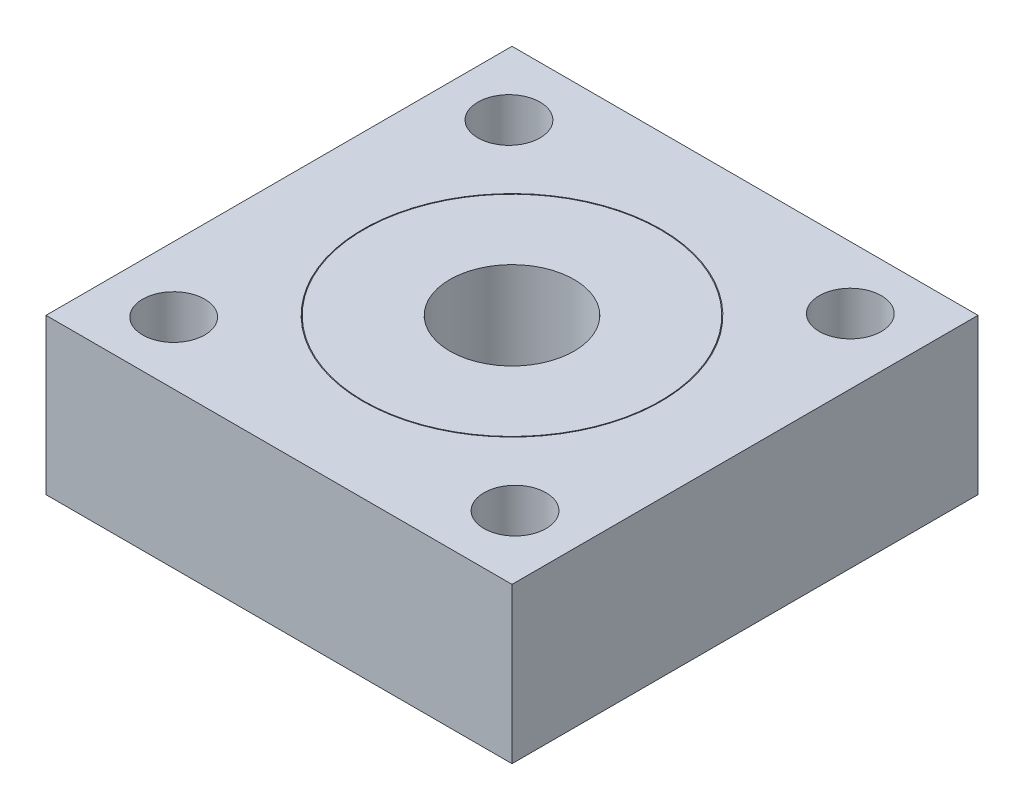
SolidWorks part; units mm, degrees
ref_plane "Front Plane" through (0, 0, 0) normal (0, 0, 1) x (1, 0, 0)
ref_plane "Top Plane" through (0, 0, 0) normal (0, 1, 0) x (1, 0, 0)
ref_plane "Right Plane" through (0, 0, 0) normal (1, 0, 0) x (0, 0, -1)
sketch "Sketch1" plane through (0, 0, 0) normal (0, 1, 0) x (1, 0, 0)
  line L1 (-15, 15) -> (15, 15)
  line L2 (-15, 15) -> (-15, -15)
  line L3 (-15, -15) -> (15, -15)
  line L4 (15, 15) -> (15, -15)
  line L5 (-15, 15) -> (15, -15) construction
  line L6 (-15, -15) -> (15, 15) construction
  point P0 (0, 0)
extrude "Boss-Extrude1" add sketch "Sketch1" along normal blind 10
sketch "Sketch2" plane through (0, 10, 0) normal (0, 1, 0) x (1, 0, 0)
  circle A0 centre (0, 0) radius 9.55
  circle A1 centre (0, 0) radius 9.6
extrude "Cut-Extrude1" cut sketch "Sketch2" against normal blind 7
sketch "Sketch3" plane through (0, 10, 0) normal (0, 1, 0) x (1, 0, 0)
  circle A0 centre (0, 0) radius 4
extrude "Cut-Extrude2" cut sketch "Sketch3" against normal blind 7
sketch "Sketch4" plane through (0, 10, 0) normal (0, 1, 0) x (1, 0, 0)
  circle A0 centre (10.7923, 10.9875) radius 2
extrude "Cut-Extrude3" cut sketch "Sketch4" against normal blind 10
pattern_circular "CirPattern1" count 4 every 90 about axis through (0, 0, 0) along (0, 1, 0) of "Cut-Extrude3"
